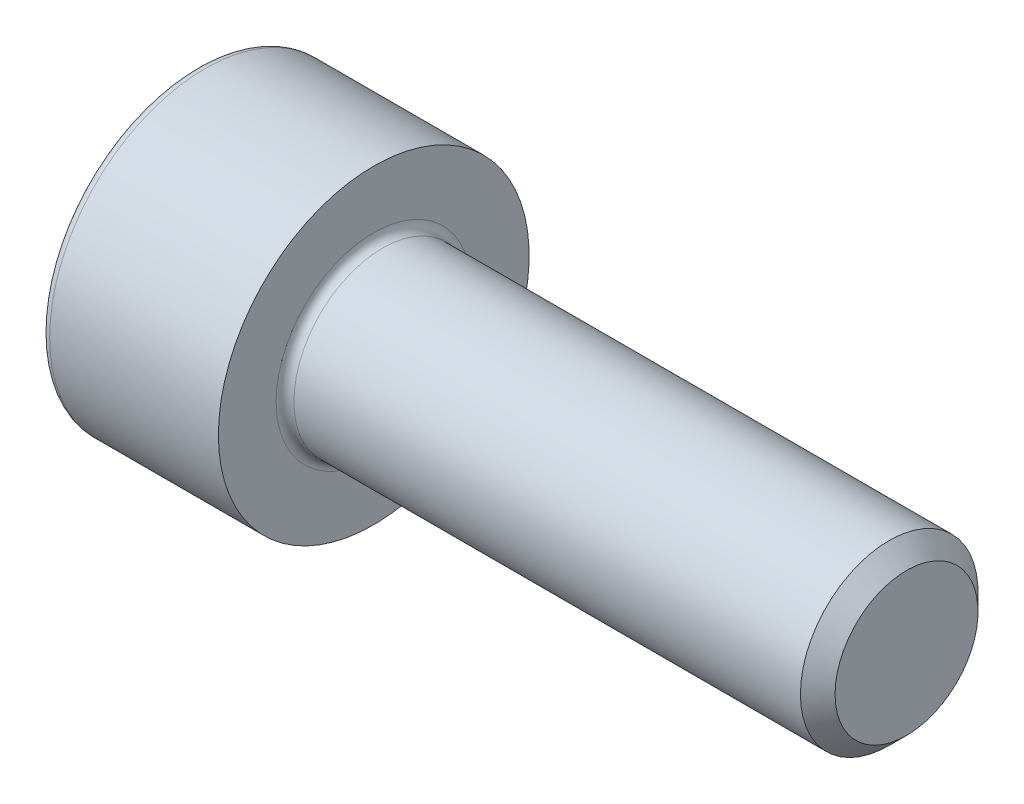
SolidWorks part; units mm, degrees
ref_plane "Plane1" through (0, 0, 0) normal (0, 0, 1) x (1, 0, 0)
ref_plane "Plane2" through (0, 0, 0) normal (0, 1, 0) x (1, 0, 0)
ref_plane "Plane3" through (0, 0, 0) normal (1, 0, 0) x (0, 0, -1)
revolve "Base-Revolve" add sketch "BodySke"
sketch "BodySke" plane through (0, 0, 0) normal (0, 0, 1) x (1, 0, 0)
  line L0 (0, 0) -> (0, 3.5)
  line L1 (0, 3.5) -> (4, 3.5)
  line L2 (4, 3.5) -> (4, 2)
  line L3 (4, 2) -> (15.61, 2)
  line L4 (16, 1.61) -> (16, 0)
  line L5 (16, 0) -> (0, 0)
  line L6 (-31.75, 0) -> (127, 0) construction
  line L8 (16, 1.61) -> (15.61, 2)
  line L10 (16, -1.61) -> (15.61, -2) construction
  line L11 (4.7, 9.525) -> (4.7, 3.175) construction
  line L12 (4, 9.525) -> (4, 3.175) construction
  line L13 (-44, 9.525) -> (-44, 3.175) construction
  dimension "Diameter" = 4
  dimension "Head_ht" = 4
  dimension "Length" = 12
  dimension "Body_ch_ang" = 45
  dimension "Head_dia" = 7
  dimension "Minor_dia" = 3.22
  dimension "Advance" = 0.7
  dimension "Thread_nom" = 12
  dimension "Thread_length" = 60
cosmetic thread "ThreadCosmetic"
fillet "Fillet1" radius 0.2 1 edges at (4, 0, 2)
fillet "Fillet2" radius 0.2 1 edges at (0, 0, 3.5)
sketch "Sketch2" plane through (0, 0, 0) normal (0, 0, 1) x (1, 0, 0)
  line L0 (0, 1.5355) -> (2, 1.5355)
  line L1 (2, 1.5355) -> (2.8865, 0)
  line L2 (-31.75, 0) -> (127, 0) construction
  line L3 (2.8865, 0) -> (0, 0)
  line L4 (0, 0) -> (0, 1.5355)
  line L6 (0, 0) -> (47.625, 0) construction
  dimension "D1" = 1.5355
  dimension "D2" = 60
  dimension "Depth" = 2
revolve "Hex-PreBroach" cut sketch "Sketch2" angle 360 about L6
sketch "Sketch3" plane through (0, 0, 0) normal (-1, 0, 0) x (0, 0.5, 0.866)
  line L0 (0.8865, 1.5355) -> (-0.8865, 1.5355)
  line L1 (-0.8865, 1.5355) -> (-1.773, 0)
  line L2 (0.8865, 1.5355) -> (1.773, 0)
  line L3 (0.8865, -1.5355) -> (1.773, 0)
  line L4 (0.8865, -1.5355) -> (-0.8865, -1.5355)
  line L5 (-0.8865, -1.5355) -> (-1.773, 0)
  dimension "D1" = 1.5355
  dimension "D2" = 1.5355
  dimension "Hex_size" = 3.071
extrude "Hex" cut sketch "Sketch3" against normal blind 2
sketch "ThdSchSke" plane through (0, 0, 0) normal (0, 0, 1) x (1, 0, 0)
  line L0 (6.1, -1.61) -> (5.8269, -2)
  line L1 (6.1, -1.61) -> (6.3731, -2)
  line L2 (6.3731, -2) -> (6.3731, -2.5)
  line L3 (-3.175, 0) -> (5.1513, 0) construction
  line L4 (0, 3.3) -> (0, -3.3) construction
  line L5 (6.3731, -2.5) -> (5.8269, -2.5)
  line L6 (5.8269, -2.5) -> (5.8269, -2)
  dimension "Thread_minor" = 3.22
  dimension "Diameter" = 4
  dimension "Start" = 6.1
  dimension "SideAngle" = 55
  dimension "VeeAngle" = 70
  dimension "Overcut" = 5
revolve "ThreadSchematic" cut sketch "ThdSchSke" angle 360 about L3
pattern_linear "ThdSchPat"
equation "\"D2@Sketch3\" = \"Hex_size@Sketch3\" / 2"
equation "\"D1@Sketch3\" = \"Hex_size@Sketch3\" / 2"
equation "\"D1@Sketch2\" = \"Hex_size@Sketch3\" / 2"
equation "\"Thread_minor@ThreadCosmetic\"  =  \"Minor_dia@BodySke\""
equation "\"Depth@Sketch2\" =  \"Key_eng@Hex\""
equation "\"Thread_length@ThreadCosmetic\" = ((sgn( (\"Length@BodySke\" - \"Advance@BodySke\" * 3.0) - \"Thread_nom@BodySke\" )-1)*( (\"Length@BodySke\" - \"Advance@BodySke\" * 3.0) - \"Thread_nom@BodySke\" ))/-2+ \"Thread_nom@BodySke\""
equation "\"Thread_minor@ThdSchSke\" = \"Minor_dia@BodySke\""
equation "\"Diameter@ThdSchSke\" = \"Diameter@BodySke\""
equation "\"Overcut@ThdSchSke\" = \"Diameter@BodySke\" * 1.25"
equation "\"Start@ThdSchSke\" = \"Head_ht@BodySke\" + \"Length@BodySke\" - \"Thread_length@ThreadCosmetic\"  '---Non-countersunk---"
equation "\"Num_threads@ThdSchPat\" = int( \"Thread_length@ThreadCosmetic\" / \"Advance@BodySke\" + 0.999 )  + 1"
equation "\"Advance@ThdSchPat\" = \"Thread_length@ThreadCosmetic\" /  (\"Num_threads@ThdSchPat\" - 1) 'relax it"
equation "\"Num_threads@ThdSchPat\" = \"Num_threads@ThdSchPat\" - sgn( \"Num_threads@ThdSchPat\" - 1) '---chamfered tips only---"
